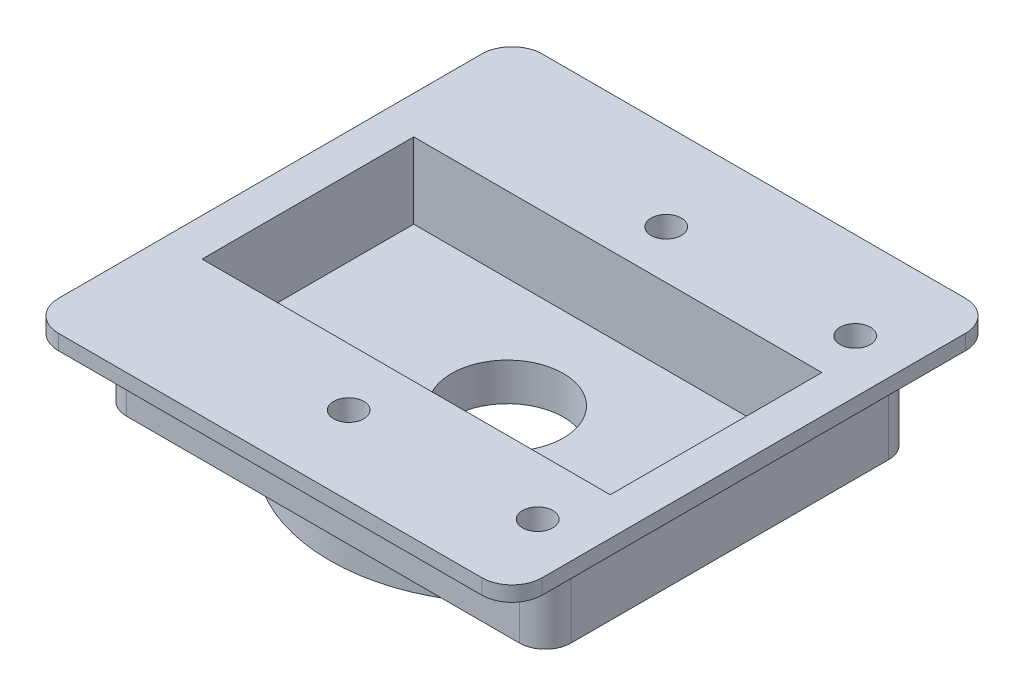
SolidWorks part; units mm, degrees
ref_plane "前视基准面" through (0, 0, 0) normal (0, 0, 1) x (1, 0, 0)
ref_plane "上视基准面" through (0, 0, 0) normal (0, 1, 0) x (1, 0, 0)
ref_plane "右视基准面" through (0, 0, 0) normal (1, 0, 0) x (0, 0, -1)
other "Configuration Table"
sketch "草图1" plane through (0, 0, 0) normal (0, 1, 0) x (1, 0, 0)
  line L1 (-40.5526, -2.4556) -> (-8.5526, -2.4556)
  line L2 (-40.5526, -2.4556) -> (-40.5526, -34.4556)
  line L3 (-40.5526, -34.4556) -> (-8.5526, -34.4556)
  line L4 (-8.5526, -2.4556) -> (-8.5526, -34.4556)
  point P4 (0, -1.547)
  point P5 (-42.5506, -2.088)
  point P6 (-40, -34.649)
  point P7 (-8.5526, -34.4556)
  dimension "D1" = 32
  dimension "D2" = 32
extrude "凸台-拉伸1" add sketch "草图1" along normal blind 1
sketch "草图3" plane through (0, 0, 0) normal (0, -1, 0) x (1, 0, 0)
  line L20 (-9.8526, 8.2556) -> (-9.8526, 29.2556)
  line L21 (-37.5526, 6.5556) -> (-11.5526, 6.5556)
  line L22 (-39.2526, 29.2556) -> (-39.2526, 8.2556)
  line L23 (-11.5526, 30.9556) -> (-37.5526, 30.9556)
  arc A20 (-9.8526, 29.2556) -> (-11.5526, 30.9556) centre (-11.5526, 29.2556) ccw
  arc A21 (-11.5526, 6.5556) -> (-9.8526, 8.2556) centre (-11.5526, 8.2556) ccw
  arc A22 (-39.2526, 8.2556) -> (-37.5526, 6.5556) centre (-37.5526, 8.2556) ccw
  arc A23 (-37.5526, 30.9556) -> (-39.2526, 29.2556) centre (-37.5526, 29.2556) ccw
extrude "凸台-拉伸2" add sketch "草图3" along normal blind 5
sketch "草图2" plane through (0, 1, 0) normal (0, 1, 0) x (1, 0, 0)
  line L0 (-8.5526, -34.4556) -> (-8.5526, -2.4556) construction
  line L1 (-11.0526, -11.4556) -> (-38.0526, -11.4556)
  line L2 (-11.0526, -11.4556) -> (-11.0526, -25.4556)
  line L3 (-11.0526, -25.4556) -> (-38.0526, -25.4556)
  line L4 (-38.0526, -11.4556) -> (-38.0526, -25.4556)
  line L5 (-8.5526, -2.4556) -> (-40.5526, -2.4556) construction
  line L6 (-40.5526, -34.4556) -> (-8.5526, -34.4556) construction
  line L7 (-40.5526, -2.4556) -> (-40.5526, -34.4556) construction
  dimension "D1" = 2.5
  dimension "D2" = 9
  dimension "D3" = 9
  dimension "D4" = 2.5
extrude "切除-拉伸1" cut sketch "草图2" against normal blind 5
sketch "草图4" plane through (0, -5, 0) normal (0, -1, 0) x (1, 0, 0)
  circle A0 centre (-24.5526, 18.7556) radius 11.7476
extrude "凸台-拉伸3" add sketch "草图4" along normal blind 2
sketch "草图5" plane through (0, -7, 0) normal (0, -1, 0) x (1, 0, 0)
  circle A0 centre (-24.5526, 18.7556) radius 4.75
  dimension "D1" = 9.5
extrude "切除-拉伸2" cut sketch "草图5" against normal blind 0.5 draft 37
sketch "草图6" plane through (0, -6.5, 0) normal (0, -1, 0) x (1, 0, 0)
  circle A0 centre (-24.5526, 18.7556) radius 3.7
  dimension "D1" = 7.4
extrude "切除-拉伸3" cut sketch "草图6" against normal through all
fillet "圆角1" radius 2 4 edges at (-40.5526, 0.5, 2.4556) (-8.5526, 0.5, 2.4556) (-40.5526, 0.5, 34.4556) (-8.5526, 0.5, 34.4556)
sketch "草图7" plane through (0, 1, 0) normal (0, 1, 0) x (1, 0, 0)
  circle A0 centre (-24.5526, -8.2556) radius 1
  circle A1 centre (-12.0526, -8.2556) radius 1
  circle A2 centre (-24.5526, -29.2556) radius 1
  circle A3 centre (-12.0526, -29.2556) radius 1
  dimension "D1" = 2
extrude "切除-拉伸4" cut sketch "草图7" against normal blind 4 draft 2
